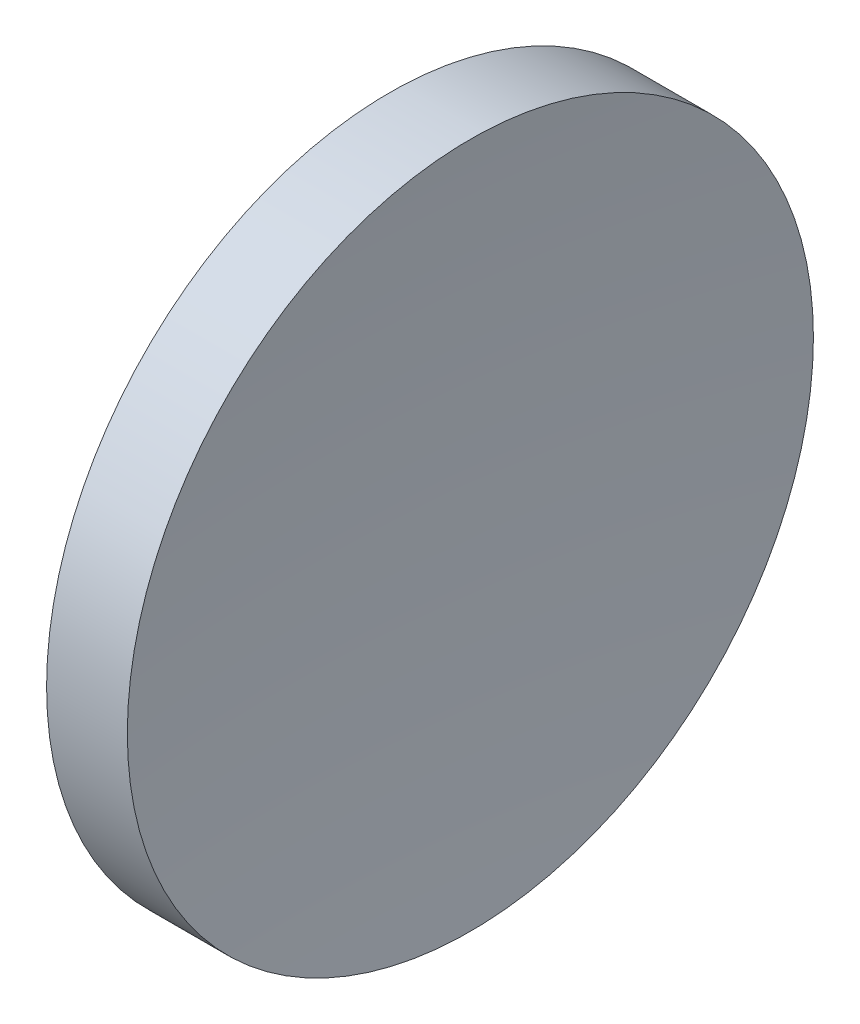
SolidWorks part; units mm, degrees
ref_plane "前视基准面" through (0, 0, 0) normal (0, 0, 1) x (1, 0, 0)
ref_plane "上视基准面" through (0, 0, 0) normal (0, 1, 0) x (1, 0, 0)
ref_plane "右视基准面" through (0, 0, 0) normal (1, 0, 0) x (0, 0, -1)
sketch "草图1" plane through (0, 0, 0) normal (0, 0, 1) x (1, 0, 0)
  line L0 (42.4499, 26.089) -> (50.324, 26.089) construction
  line L1 (44.3192, 26.089) -> (44.3192, 34.089)
  line L2 (45.8192, 26.089) -> (44.3192, 26.089)
  line L3 (44.3192, 34.089) -> (46.2021, 34.089)
  arc A0 (46.2021, 34.089) -> (45.8192, 26.089) centre (128.4391, 26.1436) ccw
revolve "旋转1" add sketch "草图1" angle 360 about L0
